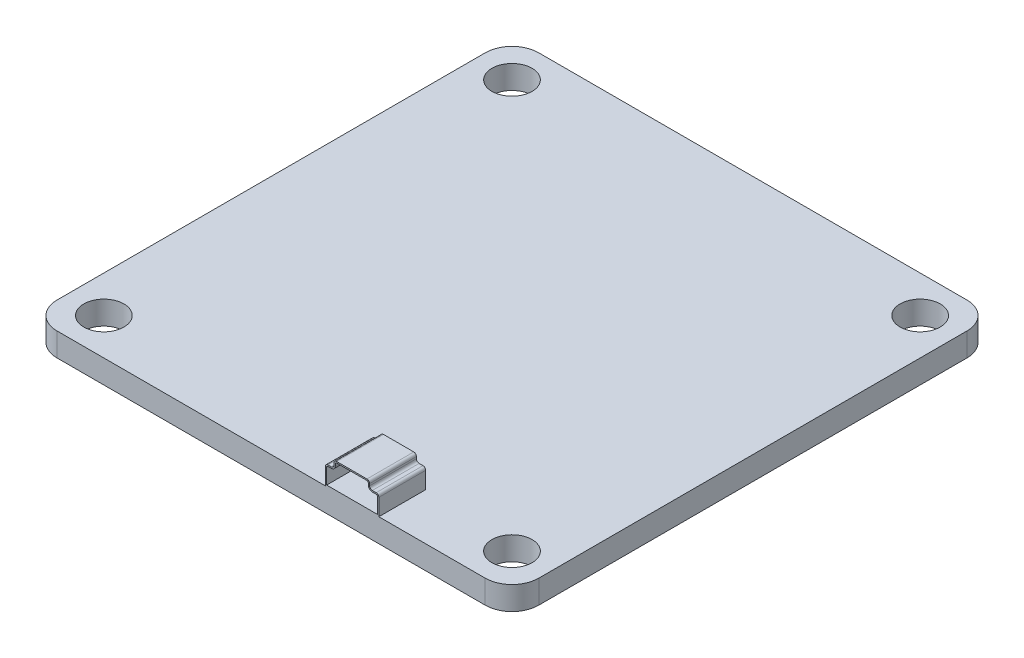
SolidWorks part; units mm, degrees
ref_plane "Front Plane" through (0, 0, 0) normal (0, 0, 1) x (1, 0, 0)
ref_plane "Top Plane" through (0, 0, 0) normal (0, 1, 0) x (1, 0, 0)
ref_plane "Right Plane" through (0, 0, 0) normal (1, 0, 0) x (0, 0, -1)
sketch "Sketch3" plane through (0, 0, 0) normal (0, 1, 0) x (1, 0, 0)
  line L1 (-16, 18) -> (16, 18)
  line L2 (-18, 16) -> (-18, -16)
  line L3 (-16, -18) -> (16, -18)
  line L4 (18, 16) -> (18, -16)
  line L5 (-18, 18) -> (18, -18) construction
  line L6 (-18, -18) -> (18, 18) construction
  line L7 (-15.25, 15.25) -> (15.25, 15.25) construction
  line L8 (-15.25, 15.25) -> (-15.25, -15.25) construction
  line L9 (-15.25, -15.25) -> (15.25, -15.25) construction
  line L10 (15.25, 15.25) -> (15.25, -15.25) construction
  line L11 (-15.25, 15.25) -> (15.25, -15.25) construction
  line L12 (-15.25, -15.25) -> (15.25, 15.25) construction
  circle A0 centre (-15.25, 15.25) radius 1.5
  circle A1 centre (15.25, 15.25) radius 1.5
  circle A2 centre (15.25, -15.25) radius 1.5
  circle A3 centre (-15.25, -15.25) radius 1.5
  arc A4 (-18, -16) -> (-16, -18) centre (-16, -16) ccw
  arc A5 (16, -18) -> (18, -16) centre (16, -16) ccw
  arc A6 (16, 18) -> (18, 16) centre (16, 16) cw
  arc A7 (-16, 18) -> (-18, 16) centre (-16, 16) ccw
  point P0 (0, 0)
  point P6 (0, 0)
  dimension "D5" = 3
  dimension "D6" = 2
  dimension "D1" = 36
  dimension "D2" = 36
  dimension "D3" = 30.5
  dimension "D4" = 30.5
extrude "Boss-Extrude1" add sketch "Sketch3" along normal blind 1.75
sketch "Sketch5" plane through (0, 0, 18) normal (0, 0, 1) x (1, 0, 0)
  line L0 (-16, 1.75) -> (16, 1.75) construction
  line L1 (4.0495, 1.75) -> (8.0495, 1.75)
  line L2 (4.0495, 1.75) -> (4.0495, 3.0065)
  line L3 (4.8962, 3.75) -> (7.1592, 3.75)
  line L4 (8.0495, 1.75) -> (8.0495, 3.0065)
  line L5 (4.6962, 3.55) -> (4.6962, 3.4065)
  line L6 (4.4962, 3.2065) -> (4.2495, 3.2065)
  line L7 (7.8495, 3.2065) -> (7.5592, 3.2065)
  line L8 (7.3592, 3.4065) -> (7.3592, 3.55)
  line L9 (4.8962, 3.65) -> (7.1592, 3.65)
  line L10 (7.2592, 3.4065) -> (7.2592, 3.55)
  line L11 (7.8495, 3.1065) -> (7.5592, 3.1065)
  line L12 (7.9495, 1.85) -> (7.9495, 3.0065)
  line L13 (4.1495, 1.85) -> (7.9495, 1.85)
  line L14 (4.1495, 1.85) -> (4.1495, 3.0065)
  line L15 (4.4962, 3.1065) -> (4.2495, 3.1065)
  line L16 (4.7962, 3.55) -> (4.7962, 3.4065)
  arc A0 (7.8495, 3.2065) -> (8.0495, 3.0065) centre (7.8495, 3.0065) cw
  arc A1 (7.5592, 3.2065) -> (7.3592, 3.4065) centre (7.5592, 3.4065) cw
  arc A2 (7.3592, 3.55) -> (7.1592, 3.75) centre (7.1592, 3.55) ccw
  arc A3 (4.6962, 3.55) -> (4.8962, 3.75) centre (4.8962, 3.55) cw
  arc A4 (4.6962, 3.4065) -> (4.4962, 3.2065) centre (4.4962, 3.4065) cw
  arc A5 (4.2495, 3.2065) -> (4.0495, 3.0065) centre (4.2495, 3.0065) ccw
  arc A6 (7.2592, 3.55) -> (7.1592, 3.65) centre (7.1592, 3.55) ccw
  arc A7 (7.5592, 3.1065) -> (7.2592, 3.4065) centre (7.5592, 3.4065) cw
  arc A8 (7.8495, 3.1065) -> (7.9495, 3.0065) centre (7.8495, 3.0065) cw
  arc A9 (4.2495, 3.1065) -> (4.1495, 3.0065) centre (4.2495, 3.0065) ccw
  arc A10 (4.7962, 3.4065) -> (4.4962, 3.1065) centre (4.4962, 3.4065) cw
  arc A11 (4.7962, 3.55) -> (4.8962, 3.65) centre (4.8962, 3.55) cw
  point P20 (4.6962, 3.2065)
  dimension "D1" = 0.2
  dimension "D2" = 0.1
extrude "Boss-Extrude2" add sketch "Sketch5" against normal blind 3
sketch "Sketch6" plane through (0, 0, 15) normal (0, 0, -1) x (-1, 0, 0)
  line L8 (-4.0495, 1.75) -> (-4.0495, 3.0065)
  line L9 (-4.2495, 3.2065) -> (-4.4962, 3.2065)
  line L10 (-4.6962, 3.4065) -> (-4.6962, 3.55)
  line L11 (-4.8962, 3.75) -> (-7.1592, 3.75)
  line L12 (-7.3592, 3.55) -> (-7.3592, 3.4065)
  line L13 (-7.5592, 3.2065) -> (-7.8495, 3.2065)
  line L14 (-8.0495, 3.0065) -> (-8.0495, 1.75)
  line L15 (-8.0495, 1.75) -> (-4.0495, 1.75)
  line L16 (-4.0495, 1.75) -> (-4.0495, 3.0065)
  line L17 (-4.2495, 3.2065) -> (-4.4962, 3.2065)
  line L18 (-4.6962, 3.4065) -> (-4.6962, 3.55)
  line L19 (-4.8962, 3.75) -> (-7.1592, 3.75)
  line L20 (-7.3592, 3.55) -> (-7.3592, 3.4065)
  line L21 (-7.5592, 3.2065) -> (-7.8495, 3.2065)
  line L22 (-8.0495, 3.0065) -> (-8.0495, 1.75)
  line L23 (-8.0495, 1.75) -> (-4.0495, 1.75)
  arc A6 (-4.0495, 3.0065) -> (-4.2495, 3.2065) centre (-4.2495, 3.0065) ccw
  arc A7 (-4.6962, 3.4065) -> (-4.4962, 3.2065) centre (-4.4962, 3.4065) ccw
  arc A8 (-4.6962, 3.55) -> (-4.8962, 3.75) centre (-4.8962, 3.55) ccw
  arc A9 (-7.1592, 3.75) -> (-7.3592, 3.55) centre (-7.1592, 3.55) ccw
  arc A10 (-7.5592, 3.2065) -> (-7.3592, 3.4065) centre (-7.5592, 3.4065) ccw
  arc A11 (-7.8495, 3.2065) -> (-8.0495, 3.0065) centre (-7.8495, 3.0065) ccw
  arc A12 (-4.0495, 3.0065) -> (-4.2495, 3.2065) centre (-4.2495, 3.0065) ccw
  arc A13 (-4.6962, 3.4065) -> (-4.4962, 3.2065) centre (-4.4962, 3.4065) ccw
  arc A14 (-4.6962, 3.55) -> (-4.8962, 3.75) centre (-4.8962, 3.55) ccw
  arc A15 (-7.1592, 3.75) -> (-7.3592, 3.55) centre (-7.1592, 3.55) ccw
  arc A16 (-7.5592, 3.2065) -> (-7.3592, 3.4065) centre (-7.5592, 3.4065) ccw
  arc A17 (-7.8495, 3.2065) -> (-8.0495, 3.0065) centre (-7.8495, 3.0065) ccw
  dimension "D1" = 0
extrude "Boss-Extrude3" add sketch "Sketch6" along normal blind 0.5
sketch "Sketch7" plane through (0, 0, 14.5) normal (0, 0, -1) x (-1, 0, 0)
  circle A3 centre (-6.978, 2.3783) radius 0.25
  circle A4 centre (-6.178, 2.3783) radius 0.25
  circle A5 centre (-5.378, 2.3783) radius 0.25
  dimension "D1" = 0.5
  dimension "D2" = 0.8
  dimension "D3" = 0.8
extrude "Cut-Extrude1" cut sketch "Sketch7" against normal blind 0.5
